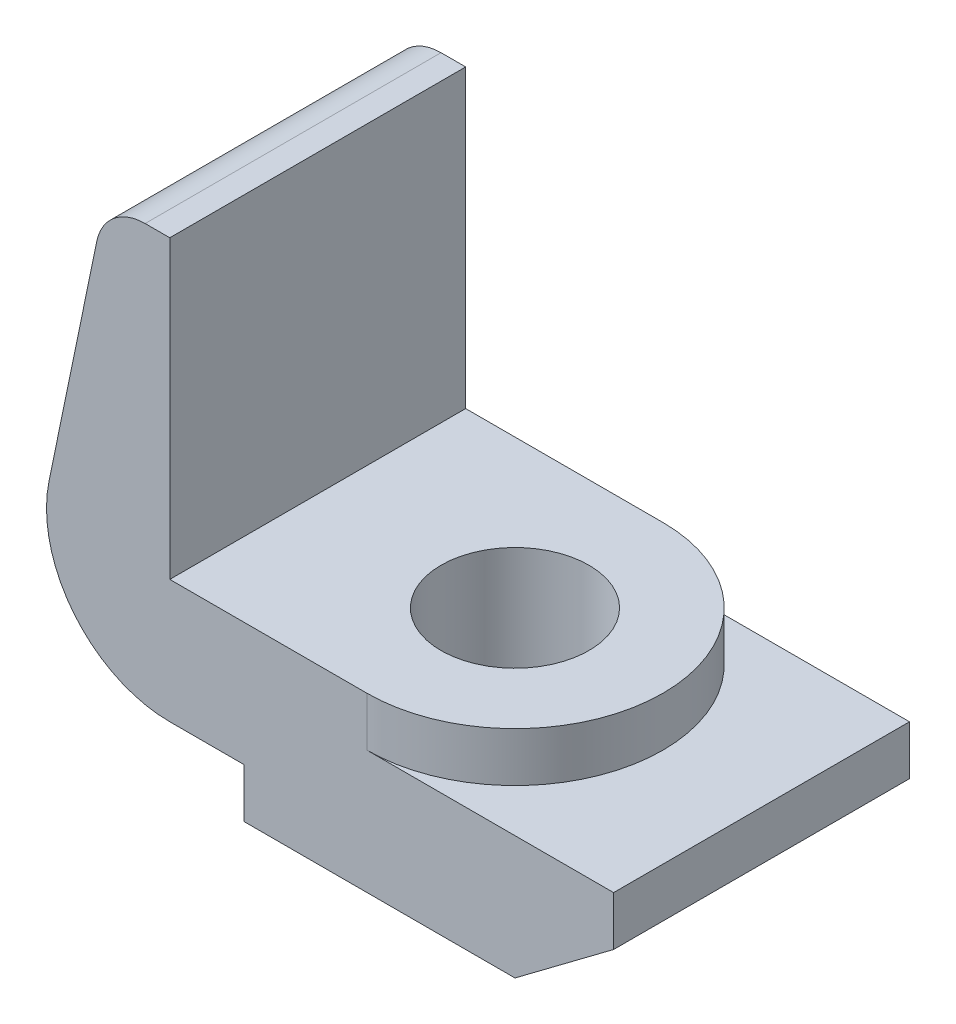
SolidWorks part; units mm, degrees
ref_plane "Front Plane" through (0, 0, 0) normal (0, 0, 1) x (1, 0, 0)
ref_plane "Top Plane" through (0, 0, 0) normal (0, 1, 0) x (1, 0, 0)
ref_plane "Right Plane" through (0, 0, 0) normal (1, 0, 0) x (0, 0, -1)
sketch "Sketch1" plane through (0, 0, 0) normal (0, 0, 1) x (1, 0, 0)
  line L0 (0, 0) -> (69.85, 0)
  line L1 (69.85, 0) -> (95.25, 19.05)
  line L2 (95.25, 19.05) -> (95.25, 31.75)
  line L3 (95.25, 31.75) -> (31.75, 31.75)
  line L4 (31.75, 31.75) -> (31.75, 44.45)
  line L5 (31.75, 44.45) -> (-19.05, 44.45)
  line L6 (-19.05, 44.45) -> (-19.05, 12.7)
  line L7 (-19.05, 12.7) -> (0, 12.7)
  line L8 (0, 12.7) -> (0, 0)
  dimension "D1" = 69.85
  dimension "D2" = 12.7
  dimension "D3" = 31.75
  dimension "D4" = 12.7
  dimension "D5" = 12.7
  dimension "D6" = 50.8
  dimension "D7" = 114.3
  dimension "D8" = 19.05
extrude "Boss-Extrude1" add sketch "Sketch1" along normal blind 76.2
sketch "Sketch2" plane through (0, 31.75, 0) normal (0, 1, 0) x (1, 0, 0)
  line L1 (31.75, -76.2) -> (31.75, 0) construction
  line L2 (95.25, -76.2) -> (31.75, -76.2) construction
  circle A1 centre (31.75, -38.1) radius 38.1
  dimension "D1" = 76.2
  dimension "D2" = 38.1
extrude "Boss-Extrude2" add sketch "Sketch2" along normal through all
sketch "Sketch3" plane through (0, 44.45, 0) normal (0, 1, 0) x (1, 0, 0)
  circle A0 centre (31.75, -38.1) radius 19.05
  arc A1 (31.75, -76.2) -> (31.75, 0) centre (31.75, -38.1) ccw construction
  dimension "D1" = 38.1
extrude "Cut-Extrude1" cut sketch "Sketch3" against normal through all
sketch "Sketch4" plane through (0, 0, 76.2) normal (0, 0, 1) x (1, 0, 0)
  line L0 (31.75, 44.45) -> (-19.05, 44.45) construction
  line L1 (-19.05, 44.45) -> (-19.05, 12.7) construction
  line L2 (-19.05, 44.45) -> (-19.05, 120.65)
  line L3 (-19.05, 120.65) -> (-25.4, 120.65)
  line L4 (-37.838, 110.5162) -> (-50.1451, 50.8655)
  line L5 (-19.05, 44.45) -> (-19.05, 12.7)
  arc A2 (-50.1451, 50.8655) -> (-19.05, 12.7) centre (-19.05, 44.45) ccw
  arc A3 (-37.838, 110.5162) -> (-25.4, 120.65) centre (-25.4, 107.95) cw
  point P11 (0, 0)
  point P14 (0, 0)
  point P15 (-17.9936, 87.0847)
  point P16 (0, 0)
  point P17 (-19.05, 43.817)
  point P18 (-19.05, 43.817)
  point P19 (-19.05, 43.384)
  point P20 (-44.2837, 58.183)
  point P21 (-19.05, 30.326)
  point P22 (-19.05, 43.817)
  point P23 (-19.05, 43.817)
  point P24 (-19.05, 43.817)
  point P25 (-19.05, 43.817)
  point P26 (-19.05, 30.5001)
  point P27 (-19.05, 43.817)
  point P28 (-19.05, 43.817)
  point P29 (-19.05, 43.817)
  point P30 (-19.05, 43.817)
  point P31 (-91.8149, 123.8212)
  point P32 (-19.05, 44.314)
  point P33 (-19.05, 44.314)
  point P34 (-19.05, 29.4647)
  dimension "D1" = 12.7
  dimension "D5" = 31.75
  dimension "D6" = 31.75
  dimension "D7" = 31.75
  dimension "D2" = 76.2
  dimension "D3" = 0
  dimension "D4" = 0
  dimension "D8" = 6.35
extrude "Boss-Extrude3" add sketch "Sketch4" against normal through all contours A2 L5 L2 L3 A3 L4
